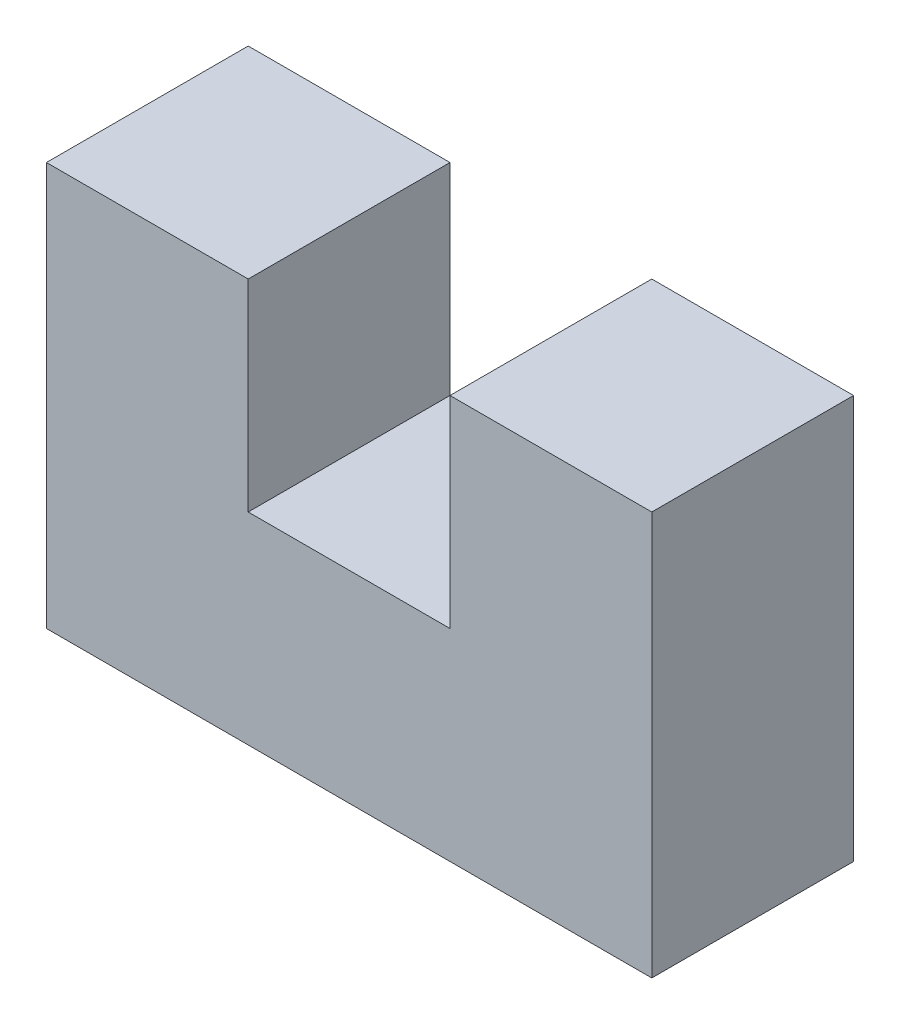
SolidWorks part; units mm, degrees
ref_plane "Front Plane" through (0, 0, 0) normal (0, 0, 1) x (1, 0, 0)
ref_plane "Top Plane" through (0, 0, 0) normal (0, 1, 0) x (1, 0, 0)
ref_plane "Right Plane" through (0, 0, 0) normal (1, 0, 0) x (0, 0, -1)
sketch "Sketch1" plane through (0, 0, 0) normal (0, 0, 1) x (1, 0, 0)
  line L95 (0, 50.8) -> (0, 0)
  line L96 (0, 0) -> (76.2, 0)
  line L97 (76.2, 0) -> (76.2, 50.8)
  line L98 (76.2, 50.8) -> (50.8, 50.8)
  line L99 (50.8, 50.8) -> (50.8, 25.4)
  line L100 (50.8, 25.4) -> (25.4, 25.4)
  line L101 (25.4, 25.4) -> (25.4, 50.8)
  line L102 (25.4, 50.8) -> (0, 50.8)
extrude "Boss-Extrude1" add sketch "Sketch1" along normal blind 25.4
